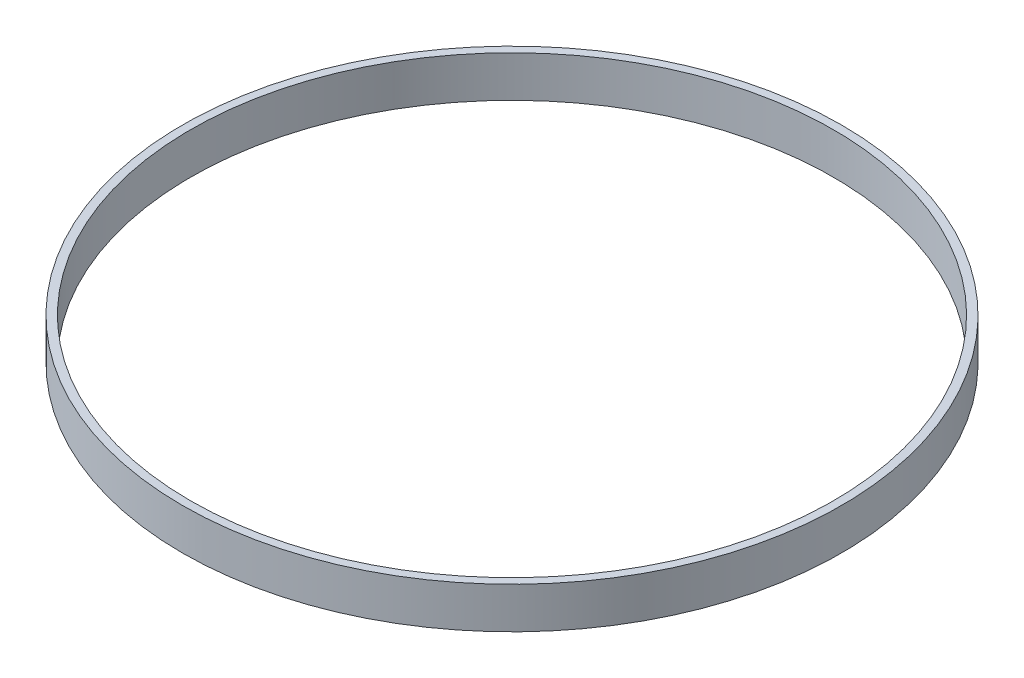
SolidWorks part; units mm, degrees
ref_plane "Front Plane" through (0, 0, 0) normal (0, 0, 1) x (1, 0, 0)
ref_plane "Top Plane" through (0, 0, 0) normal (0, 1, 0) x (1, 0, 0)
ref_plane "Right Plane" through (0, 0, 0) normal (1, 0, 0) x (0, 0, -1)
sketch "Sketch1" plane through (0, 0, 0) normal (0, 1, 0) x (1, 0, 0)
  circle A0 centre (0, 0) radius 101.6
  circle A1 centre (0, 0) radius 99.1
  dimension "D1" = 203.2
  dimension "D2" = 198.2
extrude "Boss-Extrude1" add sketch "Sketch1" along normal blind 12.7 contours A1 | A0
